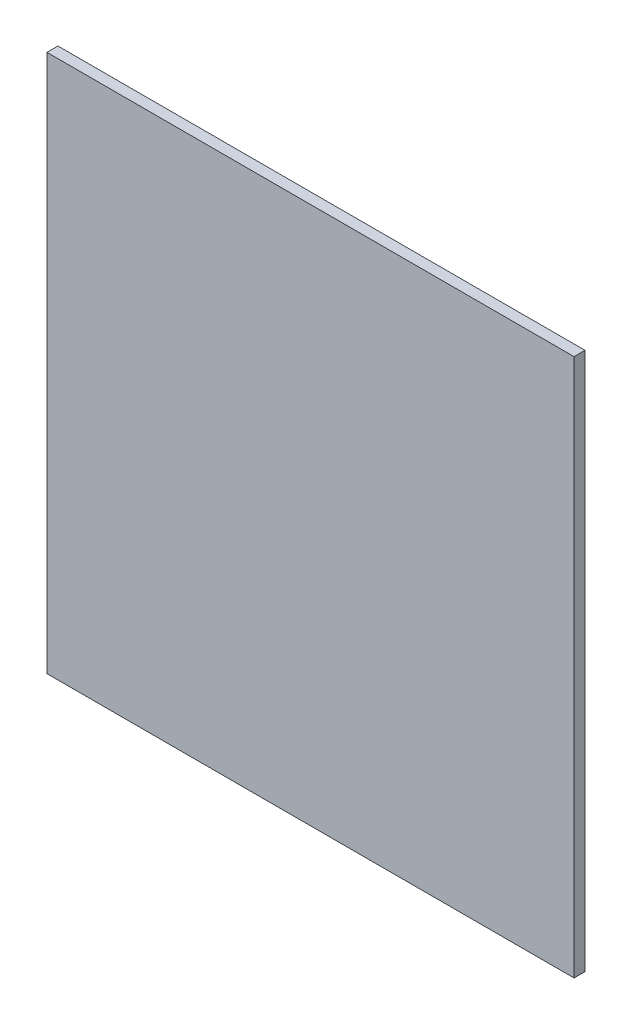
SolidWorks part; units mm, degrees
ref_plane "Front Plane" through (0, 0, 0) normal (0, 0, 1) x (1, 0, 0)
ref_plane "Top Plane" through (0, 0, 0) normal (0, 1, 0) x (1, 0, 0)
ref_plane "Right Plane" through (0, 0, 0) normal (1, 0, 0) x (0, 0, -1)
sketch "Sketch1" plane through (0, 0, 0) normal (0, 0, 1) x (1, 0, 0)
  line L1 (0, 0) -> (240, 0)
  line L2 (0, 0) -> (0, -410)
  line L3 (0, -410) -> (240, -410)
  line L4 (240, 0) -> (240, -410)
  dimension "D1" = 240
  dimension "D2" = 410
extrude "Boss-Extrude1" add sketch "Sketch1" along normal blind 5
sketch "Sketch2" plane through (0, -410, 0) normal (0, -1, 0) x (1, 0, 0)
  line L4 (0, 0) -> (240, 0)
  line L5 (240, 0) -> (240, 5)
  line L6 (240, 5) -> (0, 5)
  line L7 (0, 5) -> (0, 0)
  line L8 (0, 0) -> (240, 0)
  line L9 (240, 0) -> (240, 5)
  line L10 (240, 5) -> (0, 5)
  line L11 (0, 5) -> (0, 0)
  dimension "D1" = 0
extrude "Cut-Extrude1" cut sketch "Sketch2" against normal blind 165
